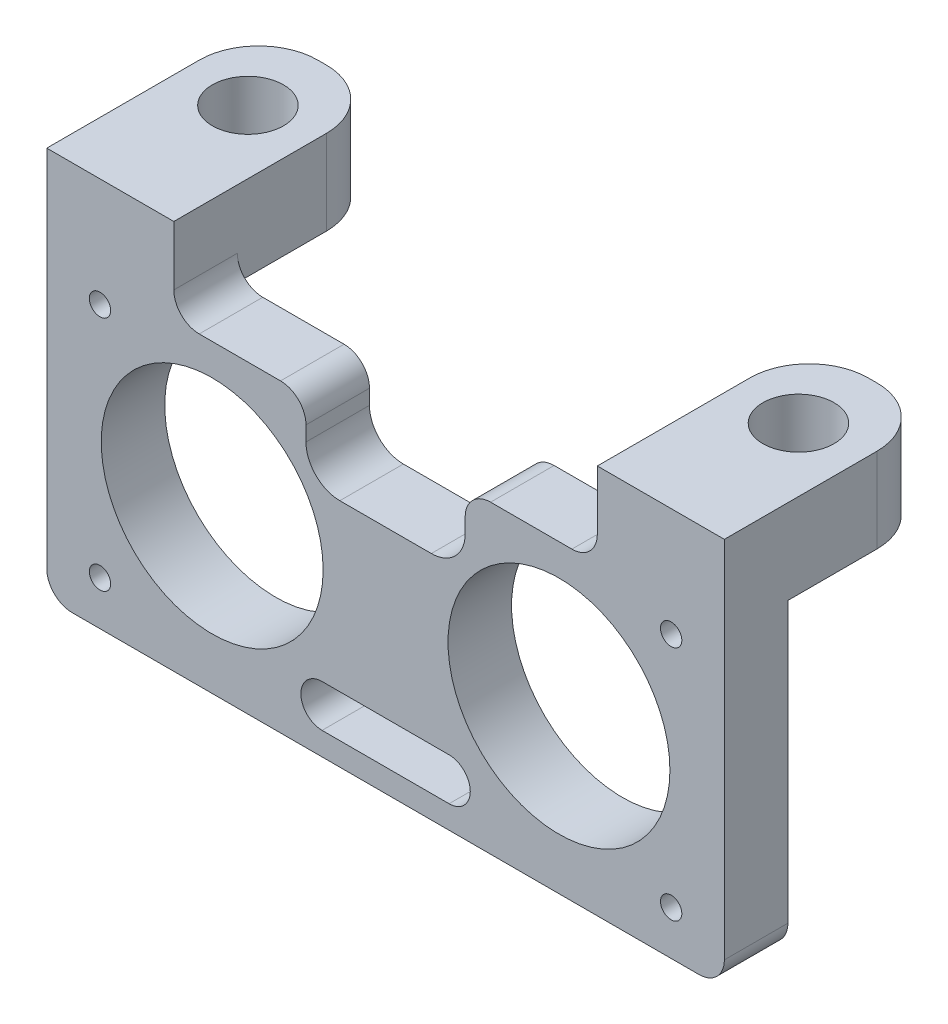
SolidWorks part; units mm, degrees
ref_plane "Front Plane" through (0, 0, 0) normal (0, 0, 1) x (1, 0, 0)
ref_plane "Top Plane" through (0, 0, 0) normal (0, 1, 0) x (1, 0, 0)
ref_plane "Right Plane" through (0, 0, 0) normal (1, 0, 0) x (0, 0, -1)
sketch "Sketch10" plane through (0, 0, 0) normal (0, 0, 1) x (1, 0, 0)
  line L0 (-21.41, 17.74) -> (-21.41, 0) construction
  line L1 (-21.41, 0) -> (21.41, 0) construction
  line L2 (21.41, 0) -> (21.41, 17.74) construction
  line L3 (21.41, 17.74) -> (-21.41, 17.74) construction
  line L4 (0, 0) -> (0, -3.312) construction
  line L5 (-13, 8.87) -> (13, 8.87) construction
  line L6 (13, 8.87) -> (21.41, 8.87) construction
  line L7 (0, 13.9911) -> (0, 0) construction
  line L8 (-4.7625, 0) -> (4.7625, 0) construction
  line L9 (-4.7625, 1.5875) -> (4.7625, 1.5875)
  line L10 (-4.7625, -1.5875) -> (4.7625, -1.5875)
  line L16 (5.969, 19.548) -> (5.969, 16.5311)
  line L17 (3.429, 13.9911) -> (-3.429, 13.9911)
  line L18 (-5.969, 16.5311) -> (-5.969, 19.548)
  line L19 (-5.969, 19.548) -> (-25.4, 19.548)
  line L20 (-25.4, 19.548) -> (-25.4, -3.312)
  line L21 (-25.4, -3.312) -> (25.4, -3.312)
  line L22 (25.4, -3.312) -> (25.4, 19.548)
  line L23 (25.4, 19.548) -> (5.969, 19.548)
  arc A0 (-4.7625, 1.5875) -> (-4.7625, -1.5875) centre (-4.7625, 0) ccw
  arc A1 (4.7625, -1.5875) -> (4.7625, 1.5875) centre (4.7625, 0) ccw
  arc A4 (3.429, 13.9911) -> (5.969, 16.5311) centre (3.429, 16.5311) ccw
  arc A5 (-5.969, 16.5311) -> (-3.429, 13.9911) centre (-3.429, 16.5311) ccw
  circle A8 centre (21.41, 17.74) radius 0.8
  circle A9 centre (21.41, 0) radius 0.8
  circle A10 centre (-21.41, 17.74) radius 0.8
  circle A11 centre (-21.41, 0) radius 0.8
  circle A12 centre (13, 8.87) radius 8.3185
  circle A13 centre (-13, 8.87) radius 8.3185
  point P31 (0, 0)
  dimension "D1" = 16.637
  dimension "D2" = 1.6
  dimension "D3" = 2.54
  dimension "D12" = 8.41
  dimension "D13" = 9.525
  dimension "D4" = 3.0169
  dimension "D5" = 6.858
  dimension "D6" = 1.808
  dimension "D7" = 17.74
  dimension "D8" = 42.82
  dimension "D9" = 50.8
  dimension "D10" = 22.86
  dimension "D11" = 26
  dimension "D14" = 3.175
extrude "Boss-Extrude1" add sketch "Sketch10" along normal blind 4.7625
sketch "Sketch11" plane through (0, 19.548, 0) normal (0, -1, 0) x (1, 0, 0)
  line L1 (25.4, 4.7625) -> (15.875, 4.7625)
  line L2 (25.4, 4.7625) -> (25.4, -11.1125)
  line L3 (25.4, -11.1125) -> (15.875, -11.1125)
  line L4 (15.875, 4.7625) -> (15.875, -11.1125)
  line L5 (-25.4, 4.7625) -> (-15.875, 4.7625)
  line L6 (-25.4, 4.7625) -> (-25.4, -11.1125)
  line L7 (-25.4, -11.1125) -> (-15.875, -11.1125)
  line L8 (-15.875, 4.7625) -> (-15.875, -11.1125)
  dimension "D1" = 9.525
  dimension "D2" = 15.875
extrude "Boss-Extrude2" add sketch "Sketch11" against normal blind 6.35 contours L2 L1 L4 L3 | L8 L7 L6 L5
fillet "Fillet1" radius 1.905 6 edges at (-25.4, -3.312, 2.3813) (-5.969, 19.548, 2.3813) (5.969, 19.548, 2.3813) (25.4, -3.312, 2.3813) (15.875, 19.548, 2.3813) (-15.875, 19.548, 2.3812)
sketch "Sketch12" plane through (0, 19.548, 0) normal (0, -1, 0) x (1, 0, 0)
  line L0 (-20.6375, -5.5563) -> (-20.6375, -11.1125) construction
  line L1 (-25.4, -11.1125) -> (-15.875, -11.1125) construction
  line L2 (-20.6375, -5.5563) -> (-15.875, -5.5563) construction
  line L3 (-15.875, 0) -> (-15.875, -11.1125) construction
  line L4 (20.6375, -5.5563) -> (20.6375, -11.1125) construction
  line L5 (25.4, -11.1125) -> (15.875, -11.1125) construction
  line L6 (25.4, -5.5563) -> (20.6375, -5.5563) construction
  line L7 (25.4, 0) -> (25.4, -11.1125) construction
  circle A0 centre (-20.6375, -5.5563) radius 2.667
  circle A1 centre (20.6375, -5.5563) radius 2.667
  dimension "D1" = 5.334
extrude "Cut-Extrude1" cut sketch "Sketch12" against normal through all
fillet "Fillet2" radius 4.445 4 edges at (-25.4, 22.723, -11.1125) (-15.875, 22.723, -11.1125) (25.4, 22.723, -11.1125) (15.875, 22.723, -11.1125)
chamfer "Chamfer1" distance 1.27 angle 45 2 edges at (20.6375, 19.548, -8.2233) (-20.6375, 19.548, -8.2233)
